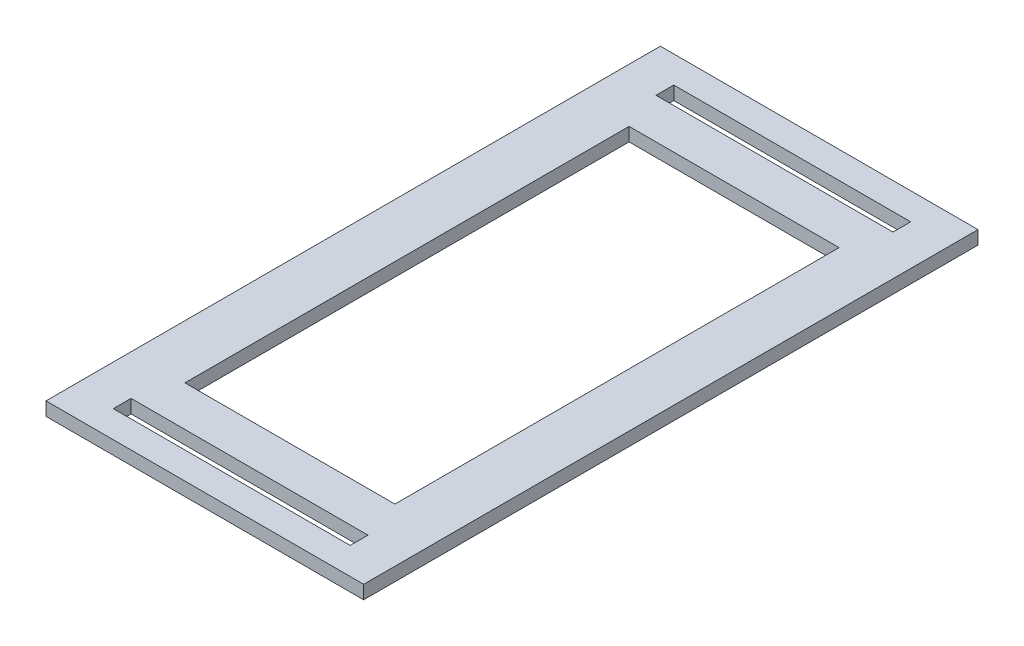
SolidWorks part; units mm, degrees
material "Acrylic (Medium-high impact)"
ref_plane "Front Plane" through (0, 0, 0) normal (0, 0, 1) x (1, 0, 0)
ref_plane "Top Plane" through (0, 0, 0) normal (0, 1, 0) x (1, 0, 0)
ref_plane "Right Plane" through (0, 0, 0) normal (1, 0, 0) x (0, 0, -1)
sketch "Sketch1" plane through (0, 0, 0) normal (0, 1, 0) x (1, 0, 0)
  line L0 (0, 52.3875) -> (0, 0) construction
  line L1 (-37.465, 72.4535) -> (37.465, 72.4535)
  line L2 (-37.465, 72.4535) -> (-37.465, -72.4535)
  line L3 (-37.465, -72.4535) -> (37.465, -72.4535)
  line L4 (37.465, 72.4535) -> (37.465, -72.4535)
  line L5 (-27.94, -61.9125) -> (27.94, -61.9125)
  line L6 (-27.94, -61.9125) -> (-27.94, -66.1035)
  line L7 (-27.94, -66.1035) -> (27.94, -66.1035)
  line L8 (27.94, -61.9125) -> (27.94, -66.1035)
  line L9 (-27.94, 66.1035) -> (27.94, 66.1035)
  line L10 (-27.94, 66.1035) -> (-27.94, 61.9125)
  line L11 (-27.94, 61.9125) -> (27.94, 61.9125)
  line L12 (27.94, 66.1035) -> (27.94, 61.9125)
  line L13 (-24.765, 52.3875) -> (24.765, 52.3875)
  line L14 (-24.765, 52.3875) -> (-24.765, -52.3875)
  line L15 (-24.765, -52.3875) -> (24.765, -52.3875)
  line L16 (24.765, 52.3875) -> (24.765, -52.3875)
  line L17 (-37.465, 0) -> (0, 0) construction
  point P4 (-37.465, 0)
  point P6 (0, 72.4535)
  point P11 (0, -61.9125)
  point P16 (0, 61.9125)
  point P23 (-24.765, 0)
  dimension "D1" = 55.88
  dimension "D2" = 4.191
  dimension "D3" = 6.35
  dimension "D8" = 9.525
  dimension "D4" = 123.825
  dimension "D5" = 6.35
  dimension "D6" = 3.175
  dimension "D7" = 9.525
extrude "Boss-Extrude1" add sketch "Sketch1" along normal blind 3.175
sketch "Sketch2" plane through (0, 3.175, 0) normal (0, 1, 0) x (1, 0, 0)
  line L0 (-37.465, -61.9125) -> (-37.465, 61.9125)
  line L1 (-37.465, 72.4535) -> (-37.465, -72.4535) construction
  line L2 (-19.05, 0) -> (19.05, 0)
  line L3 (37.465, -72.4535) -> (37.465, 72.4535) construction
  line L4 (37.465, -61.9125) -> (37.465, 61.9125)
  line L5 (-1.7463, 0) -> (1.7463, 0) construction
  arc A0 (-37.465, -61.9125) -> (-31.75, -42.6983) centre (-2.3077, -61.9125) cw
  arc A1 (-31.75, -42.6983) -> (-31.75, 42.6983) centre (-97.1773, 0) ccw
  arc A2 (31.75, 42.6983) -> (31.75, -42.6983) centre (97.1773, 0) ccw
  arc A3 (31.75, -42.6983) -> (37.465, -61.9125) centre (2.3077, -61.9125) cw
  arc A4 (31.75, 42.6983) -> (37.465, 61.9125) centre (2.3077, 61.9125) ccw
  arc A5 (-37.465, 61.9125) -> (-31.75, 42.6983) centre (-2.3077, 61.9125) ccw
  point P25 (37.465, 0)
  point P26 (-37.465, 0)
  line M2 (-37.465, 72.4535) -> (-37.465, -72.4535)
  line M4 (37.465, -72.4535) -> (37.465, 72.4535)
  dimension "D2" = 63.5
  dimension "D1" = 38.1
extrude "Cut-Extrude1" [suppressed] cut sketch "Sketch2" against normal through all contours A5 A0 A1 M2 | A4 A2 A3 M4
equation "\"bottomThickness\"= .25in"
equation "\"wallThickness\"= .125in"
equation "\"D2@Sketch1\"=\"wallThickness\"+.04"
equation "\"D1@Boss-Extrude1\"=\"wallThickness\""
